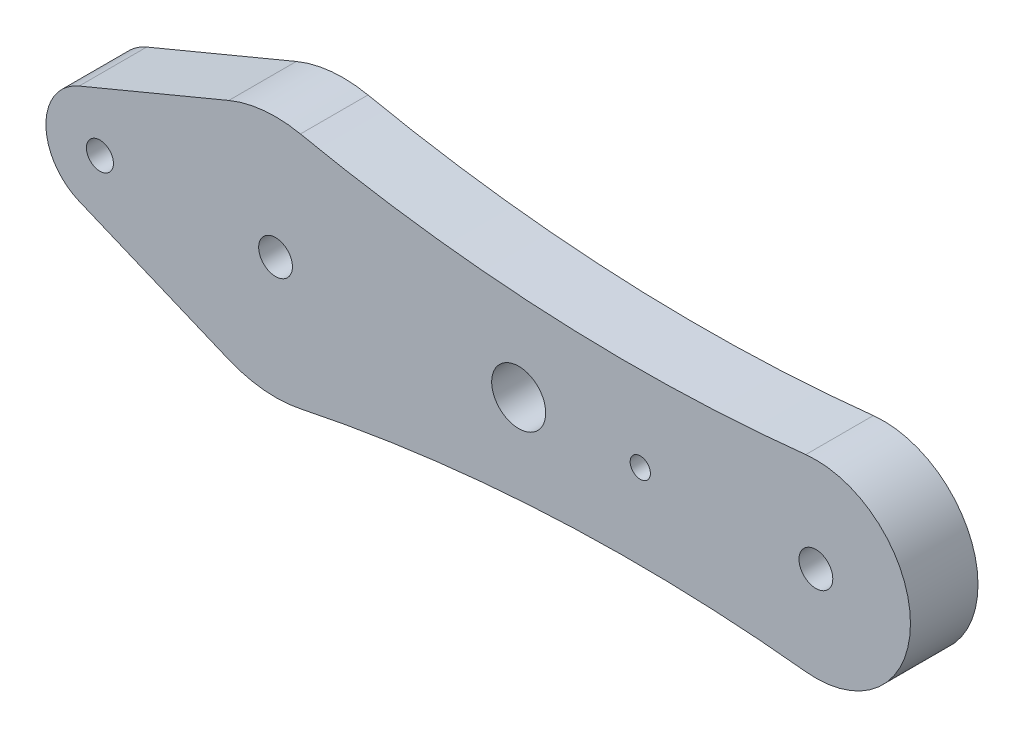
SolidWorks part; units mm, degrees
material "PMMA"
ref_plane "Front Plane" through (0, 0, 0) normal (0, 0, 1) x (1, 0, 0)
ref_plane "Top Plane" through (0, 0, 0) normal (0, 1, 0) x (1, 0, 0)
ref_plane "Right Plane" through (0, 0, 0) normal (1, 0, 0) x (0, 0, -1)
sketch "Sketch1" plane through (0, 0, 0) normal (0, 0, 1) x (1, 0, 0)
  line L0 (0, 0) -> (40, 0) construction
  line L1 (0, 0) -> (-13, 0) construction
  line L2 (-14.5385, 3.6923) -> (-3.4615, 8.3077)
  line L3 (-14.5385, -3.6923) -> (-3.4615, -8.3077)
  circle A0 centre (0, 0) radius 1.25
  circle A1 centre (40, 0) radius 1.25
  circle A2 centre (-13, 0) radius 1
  circle A3 centre (18, 0) radius 2
  circle A4 centre (27, 0) radius 0.75
  arc A7 (39.2504, -6.9597) -> (39.2504, 6.9597) centre (40, 0) ccw
  arc A8 (-3.4615, -8.3077) -> (1.8419, -8.8095) centre (0, 0) ccw
  arc A9 (-14.5385, 3.6923) -> (-14.5385, -3.6923) centre (-13, 0) ccw
  arc A10 (1.8419, -8.8095) -> (39.2504, -6.9597) centre (26.4, -126.2697) cw
  arc A11 (1.8419, 8.8095) -> (39.2504, 6.9597) centre (26.4, 126.2697) ccw
  arc A12 (1.8419, 8.8095) -> (-3.4615, 8.3077) centre (0, 0) ccw
  dimension "D1" = 2.5
  dimension "D2" = 2.5
  dimension "D3" = 1.5
  dimension "D4" = 4
  dimension "D5" = 2
  dimension "D8" = 14
  dimension "D11" = 18
  dimension "D12" = 8
  dimension "D13" = 120
  dimension "D14" = 120
  dimension "D6" = 40
  dimension "D7" = 27
  dimension "D9" = 18
  dimension "D10" = 13
extrude "Boss-Extrude1" add sketch "Sketch1" along normal blind 5
cosmetic thread "Cosmetic Thread1" parameters "D2"=3
cosmetic thread "Cosmetic Thread2" parameters "D2"=3
